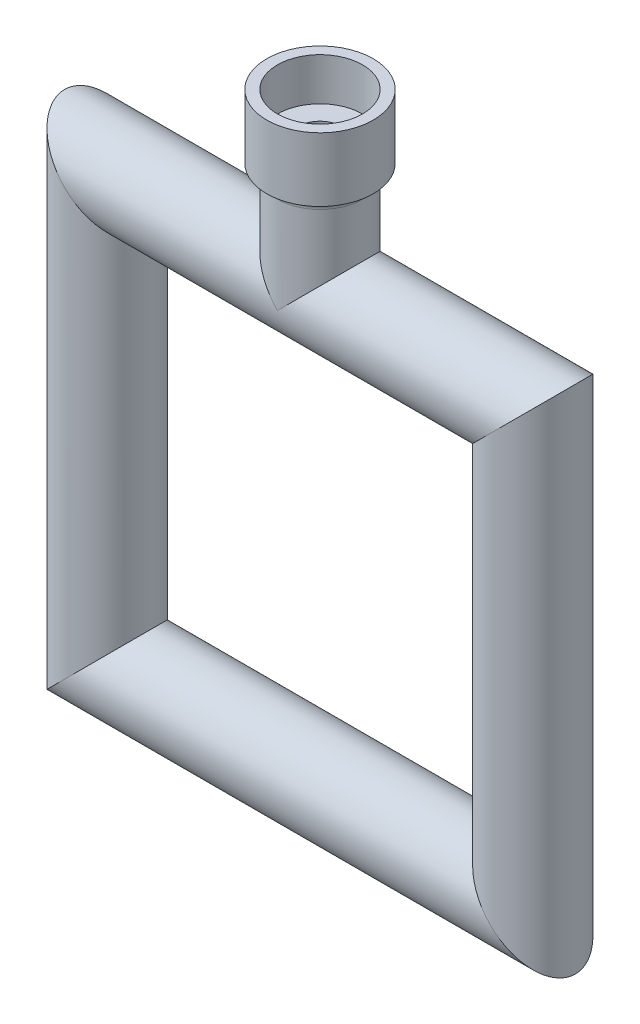
SolidWorks part; units mm, degrees
ref_plane "Piano frontale" through (0, 0, 0) normal (0, 0, 1) x (1, 0, 0)
ref_plane "Piano superiore" through (0, 0, 0) normal (0, 1, 0) x (1, 0, 0)
ref_plane "Piano destro" through (0, 0, 0) normal (1, 0, 0) x (0, 0, -1)
sketch "Schizzo1" plane through (0, 0, 0) normal (0, 0, 1) x (1, 0, 0)
  line L1 (-132.0625, 77.7082) -> (-212.0625, 77.7082)
  line L2 (-132.0625, 77.7082) -> (-132.0625, -2.2918)
  line L3 (-132.0625, -2.2918) -> (-212.0625, -2.2918)
  line L4 (-212.0625, 77.7082) -> (-212.0625, -2.2918)
  dimension "D1" = 80
  dimension "D4" = 80
sweep "Sweep5" add path "Schizzo1" circular profile diameter 16 parameters "D3"=16
ref_plane "Piano1" through (0, 0, 0) normal (0, 0, -1) x (-1, 0, 0)
ref_plane "Piano2" through (-132.0625, 0, 0) normal (1, 0, 0) x (0, -1, 0)
ref_plane "Piano4" through (-172.0625, 0, 0) normal (1, 0, 0) x (0, -1, 0)
sketch "Schizzo14" plane through (-172.0625, 0, 0) normal (1, 0, 0) x (0, -1, 0)
  line L0 (-29.5524, 0) -> (-218.357, 0) construction
  line L1 (-77.7082, 0) -> (-101.7082, 0)
  line L2 (-101.7082, 0) -> (-101.7082, 8)
  line L3 (-101.7082, 8) -> (-109.7082, 8)
  line L4 (-109.7082, 8) -> (-109.7082, 10)
  line L5 (-109.7082, 10) -> (-97.7082, 10)
  line L6 (-97.7082, 10) -> (-97.7082, 9.9)
  line L7 (-95.8082, 8) -> (-77.7082, 8)
  line L8 (-77.7082, 8) -> (-77.7082, 0)
  arc A0 (-97.7082, 9.9) -> (-95.8082, 8) centre (-95.8082, 9.9) ccw
  point P14 (-97.7082, 8)
  dimension "D7" = 1.9
  dimension "D1" = 8
  dimension "D2" = 2
  dimension "D3" = 8
  dimension "D4" = 20
  dimension "D5" = 12
  dimension "D6" = 8
revolve "Rivoluzione1" add sketch "Schizzo14" angle 360 about L0
sketch "Schizzo15" plane through (0, 101.7082, 0) normal (0, 1, 0) x (1, 0, 0)
  circle A0 centre (-172.0625, 0) radius 4
  dimension "D1" = 8
extrude "Taglio-Estrusione1" cut sketch "Schizzo15" against normal up to next
